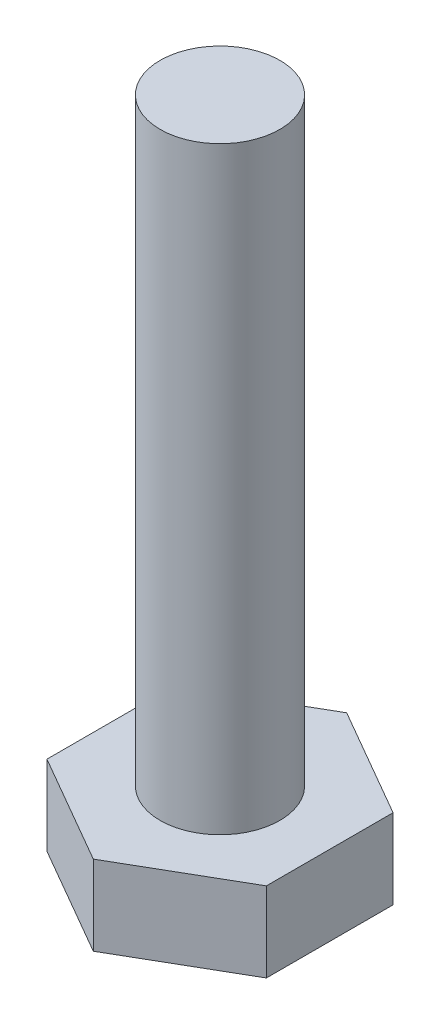
SolidWorks part; units mm, degrees
ref_plane "Спереди" through (0, 0, 0) normal (0, 0, 1) x (1, 0, 0)
ref_plane "Сверху" through (0, 0, 0) normal (0, 1, 0) x (1, 0, 0)
ref_plane "Справа" through (0, 0, 0) normal (1, 0, 0) x (0, 0, -1)
sketch "Эскиз1" plane through (0, 0, 0) normal (0, 1, 0) x (1, 0, 0)
  line L0 (0, 3.1754) -> (0, 0) construction
  line L1 (0, 3.1754) -> (-2.75, 1.5877)
  line L2 (-2.75, 1.5877) -> (-2.75, -1.5877)
  line L3 (-2.75, -1.5877) -> (0, -3.1754)
  line L4 (0, -3.1754) -> (2.75, -1.5877)
  line L5 (2.75, -1.5877) -> (2.75, 1.5877)
  line L6 (2.75, 1.5877) -> (0, 3.1754)
  circle A0 centre (0, 0) radius 2.75 construction
  dimension "D1" = 5.5
extrude "Бобышка-Вытянуть1" add sketch "Эскиз1" along normal blind 2
sketch "Эскиз2" plane through (0, 2, 0) normal (0, 1, 0) x (1, 0, 0)
  circle A0 centre (0, 0) radius 1.5
  dimension "D1" = 3
extrude "Бобышка-Вытянуть2" add sketch "Эскиз2" along normal blind 15
sketch "Эскиз3" plane through (0, 0, 0) normal (0, 0, 1) x (1, 0, 0)
  line L0 (1.5, 7) -> (-1.5, 7) construction
  line L1 (1.5, 2) -> (1.5, 17) construction
  line L2 (-1.5, 17) -> (-1.5, 2) construction
  line L3 (1.5, 17) -> (-1.5, 17) construction
  dimension "D1" = 10
ref_plane "Плоскость1" through (0, 7, 0) normal (0, 1, 0) x (1, 0, 0)
